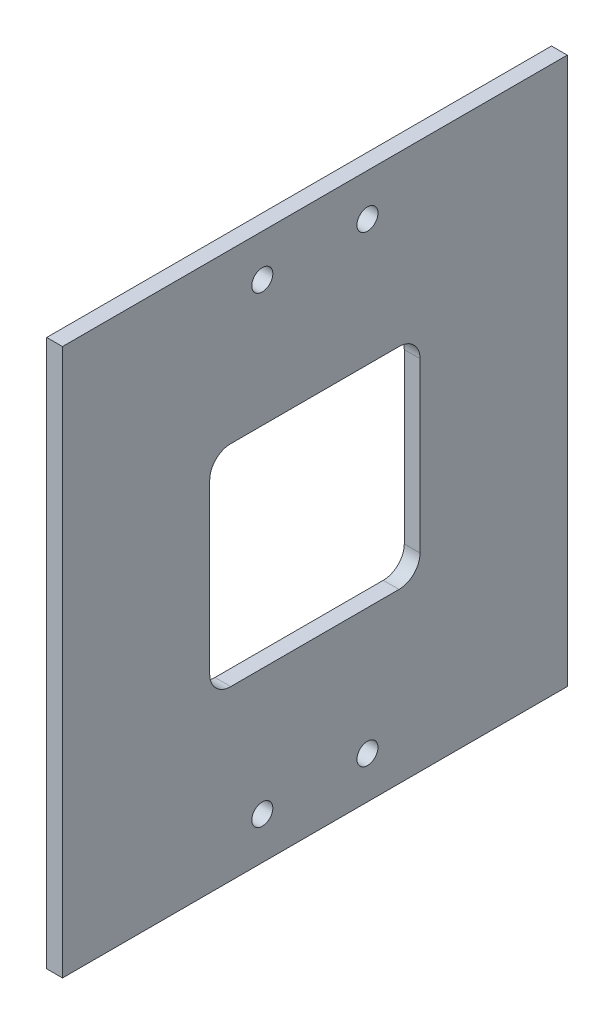
SolidWorks part; units mm, degrees
material "ASTM A36 Steel"
ref_plane "Front Plane" through (0, 0, 0) normal (0, 0, 1) x (1, 0, 0)
ref_plane "Top Plane" through (0, 0, 0) normal (0, 1, 0) x (1, 0, 0)
ref_plane "Right Plane" through (0, 0, 0) normal (1, 0, 0) x (0, 0, -1)
sketch "Sketch1" plane through (0, 0, 0) normal (1, 0, 0) x (0, 0, -1)
  line L0 (0, 2.6194) -> (0, -2.6194) construction
  line L1 (152.4, 82.55) -> (0, 82.55)
  line L2 (152.4, 82.55) -> (152.4, -82.55)
  line L3 (152.4, -82.55) -> (0, -82.55)
  line L4 (0, 82.55) -> (0, -82.55)
  line L5 (152.4, 82.55) -> (0, -82.55) construction
  line L6 (152.4, -82.55) -> (0, 82.55) construction
  line L7 (2.6194, 0) -> (-2.6194, 0) construction
  point P0 (76.2, 0)
  dimension "D1" = 152.4
  dimension "D2" = 165.1
extrude "Boss-Extrude1" add sketch "Sketch1" along normal blind 4.7625
sketch "Sketch2" plane through (0, 0, 0) normal (-1, 0, 0) x (0, 0, 1)
  line L0 (-107.95, 25.4) -> (-107.95, -25.4)
  line L1 (-101.6, -31.75) -> (-50.8, -31.75)
  line L2 (-44.45, -25.4) -> (-44.45, 25.4)
  line L3 (-50.8, 31.75) -> (-101.6, 31.75)
  line L4 (-76.2, 31.75) -> (-76.2, -31.75) construction
  line L5 (0, 0) -> (-152.4, 0)
  line L6 (-152.4, -82.55) -> (-152.4, 82.55) construction
  arc A0 (-107.95, -25.4) -> (-101.6, -31.75) centre (-101.6, -25.4) ccw
  arc A1 (-50.8, -31.75) -> (-44.45, -25.4) centre (-50.8, -25.4) ccw
  arc A2 (-44.45, 25.4) -> (-50.8, 31.75) centre (-50.8, 25.4) ccw
  arc A3 (-101.6, 31.75) -> (-107.95, 25.4) centre (-101.6, 25.4) ccw
  point P19 (-76.2, 0)
  dimension "D1" = 6.35
  dimension "D2" = 63.5
  dimension "D3" = 63.5
extrude "Cut-Extrude1" cut sketch "Sketch2" against normal through all contours L4 L5 L0 A0 L1 | L4 L3 A3 L0 L5 | L3 L4 L5 L2 A2 | L5 L4 L1 A1 L2
sketch "Sketch3" plane through (0, 0, 0) normal (-1, 0, 0) x (0, 0, 1)
  line L0 (-76.2, 82.55) -> (-76.2, -82.55) construction
  line L1 (-152.4, 82.55) -> (0, 82.55) construction
  line L2 (0, -82.55) -> (-152.4, -82.55) construction
  line L3 (-92.075, -69.85) -> (-60.325, -69.85) construction
  line L4 (-92.075, 69.85) -> (-60.325, 69.85) construction
  circle A0 centre (-60.325, 69.85) radius 3.175
  circle A1 centre (-92.075, 69.85) radius 3.175
  circle A2 centre (-92.075, -69.85) radius 3.175
  circle A3 centre (-60.325, -69.85) radius 3.175
  point P10 (-76.2, 69.85)
  point P11 (-76.2, -69.85)
  dimension "D1" = 6.35
  dimension "D2" = 12.7
  dimension "D3" = 31.75
  dimension "D4" = 12.7
extrude "Cut-Extrude2" cut sketch "Sketch3" against normal through all
